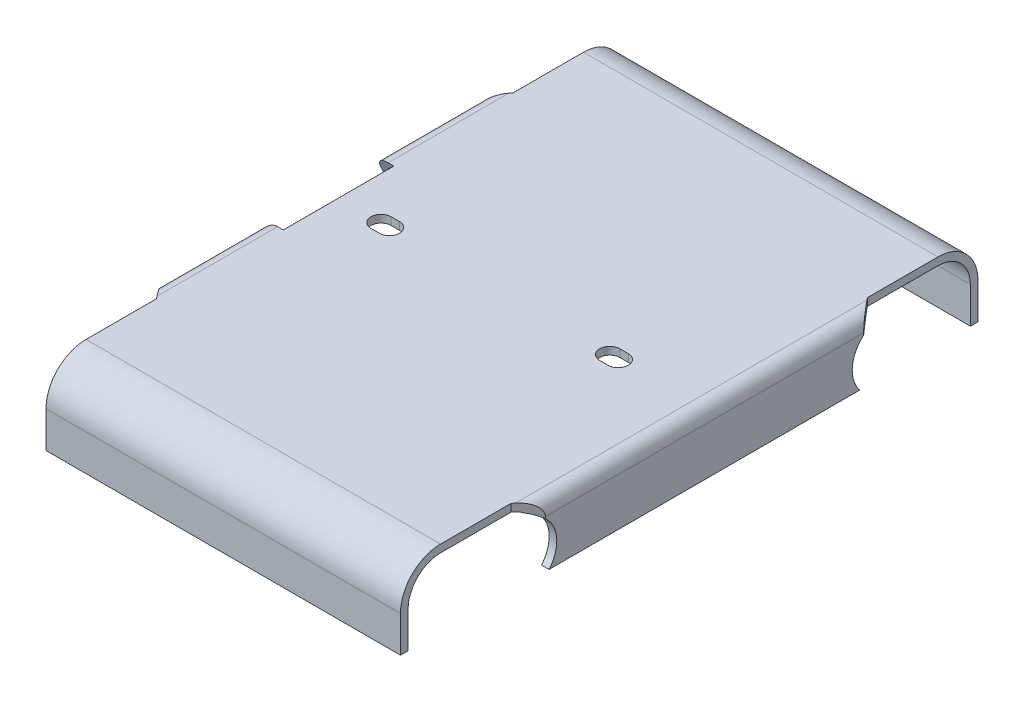
SolidWorks part; units mm, degrees
ref_plane "Plan de face" through (0, 0, 0) normal (0, 0, 1) x (1, 0, 0)
ref_plane "Plan de dessus" through (0, 0, 0) normal (0, 1, 0) x (1, 0, 0)
ref_plane "Plan de droite" through (0, 0, 0) normal (1, 0, 0) x (0, 0, -1)
sketch "Esquisse1" plane through (0, 0, 0) normal (0, 1, 0) x (1, 0, 0)
  line L0 (-60.4921, 0) -> (63.4192, 0) construction
  line L1 (-50.5, -75.75) -> (50.5, -75.75)
  line L2 (-50.5, -75.75) -> (-50.5, 75.75)
  line L3 (-50.5, 75.75) -> (50.5, 75.75)
  line L4 (50.5, -75.75) -> (50.5, 75.75)
  line L5 (0, 0) -> (0, 85.0821) construction
  dimension "D1" = 151.5
  dimension "D2" = 101
extrude "Extrusion1" add sketch "Esquisse1" against normal blind 20
fillet "Congé2" radius 10.5 2 edges at (0, 0, -75.75) (0, 0, 75.75)
fillet "Congé3" radius 3.5 10 edges at (-50.5, 0, 0) (50.5, 0, 0) (-50.5, -3.0754, 72.6746) (-50.5, -3.0754, -72.6746) (50.5, -3.0754, 72.6746) (50.5, -3.0754, -72.6746) (-50.5, -15.25, -75.75) (50.5, -15.25, -75.75) (50.5, -15.25, 75.75) (-50.5, -15.25, 75.75)
shell "Coque1" thickness 2
sketch "Esquisse5" plane through (0, 0, 0) normal (0, 1, 0) x (-1, 0, 0)
  line L0 (54.4782, 0) -> (-63.9785, 0) construction
  line L1 (47, -75.75) -> (-47, -75.75) construction
  line L2 (-46.5, -75.75) -> (-50.5, -75.75)
  line L3 (-46.5, -75.75) -> (-46.5, -46.75)
  line L5 (-50.5, -75.75) -> (-50.5, -41.75)
  line L6 (-46.5, -46.75) -> (-50.5, -41.75)
  line L7 (-50.5, -65.25) -> (-50.5, 65.25) construction
  line L8 (-46.5, 46.75) -> (-50.5, 41.75)
  line L9 (-50.5, 75.75) -> (-50.5, 41.75)
  line L10 (-46.5, 75.75) -> (-46.5, 46.75)
  line L11 (-46.5, 75.75) -> (-50.5, 75.75)
  line L12 (0, 0) -> (0, -89.9597) construction
  line L13 (46.5, 75.75) -> (50.5, 75.75)
  line L14 (46.5, 75.75) -> (46.5, 46.75)
  line L15 (50.5, 75.75) -> (50.5, 41.75)
  line L16 (46.5, 46.75) -> (50.5, 41.75)
  line L17 (46.5, -46.75) -> (50.5, -41.75)
  line L18 (50.5, -75.75) -> (50.5, -41.75)
  line L19 (46.5, -75.75) -> (46.5, -46.75)
  line L20 (46.5, -75.75) -> (50.5, -75.75)
  dimension "D1" = 4
  dimension "D2" = 34
  dimension "D3" = 5
extrude "Enlèv. mat.-Extru.4" cut sketch "Esquisse5" against normal through all
sketch "Esquisse2" plane through (0, 0, 0) normal (1, 0, 0) x (0, 0, -1)
  line L0 (0, 15.0146) -> (0, -24.9029) construction
  line L1 (-73.75, -10.5) -> (-73.75, -20)
  line L2 (-65.25, -2) -> (-47.25, -2)
  line L3 (-73.75, -20) -> (73.75, -20)
  line L5 (65.25, -2) -> (47.25, -2)
  line L6 (73.75, -10.5) -> (73.75, -20)
  line L7 (-41.75, -20) -> (41.75, -20) construction
  line L9 (-40.7693, -16) -> (40.7693, -16)
  line L10 (46.125, 0) -> (-46.125, 0) construction
  arc A0 (-65.25, -2) -> (-73.75, -10.5) centre (-65.25, -10.5) ccw
  arc A2 (-40.7693, -16) -> (-47.25, -2) centre (-47.25, -10.5) ccw
  arc A3 (40.7693, -16) -> (47.25, -2) centre (47.25, -10.5) cw
  arc A4 (65.25, -2) -> (73.75, -10.5) centre (65.25, -10.5) cw
  arc A5 (-65.25, -2) -> (-73.75, -10.5) centre (-65.25, -10.5) ccw construction
  dimension "D1" = 35
  dimension "D2" = 16
extrude "Enlèv. mat.-Extru.1" cut sketch "Esquisse2" against normal through all and the other way through all
sketch "Esquisse3" plane through (-50.5, 0, 0) normal (-1, 0, 0) x (0, 0, 1)
  line L0 (0, 7.4155) -> (0, -20.611) construction
  line L1 (-17.75, -16) -> (-17.75, -7)
  line L2 (-40.7693, -16) -> (40.7693, -16) construction
  line L3 (-17.75, -7) -> (-14.5, 0)
  line L4 (-46.125, 0) -> (46.125, 0) construction
  line L5 (17.75, -16) -> (17.75, -7)
  line L6 (17.75, -7) -> (14.5, 0)
  line L7 (-14.5, 0) -> (14.5, 0)
  line L8 (-17.75, -16) -> (17.75, -16)
  dimension "D1" = 35.5
  dimension "D2" = 29
  dimension "D3" = 9
extrude "Enlèv. mat.-Extru.2" cut sketch "Esquisse3" against normal blind 5
sketch "Esquisse6" plane through (0, 0, 0) normal (0, 1, 0) x (-1, 0, 0)
  line L0 (58.0409, 0) -> (-65.463, 0) construction
  line L1 (33.25, -8.7006) -> (33.25, 6.2394) construction
  line L2 (-25.65, 2.65) -> (-27.85, 2.65)
  line L3 (-50.5, -41.75) -> (-50.5, 41.75) construction
  line L4 (-25.65, -2.65) -> (-27.85, -2.65)
  line L5 (-26.75, -8.7006) -> (-26.75, 6.2394) construction
  line L6 (32.15, -2.65) -> (34.35, -2.65)
  line L7 (32.15, 2.65) -> (34.35, 2.65)
  arc A0 (-27.85, -2.65) -> (-27.85, 2.65) centre (-27.85, 0) cw
  arc A1 (-25.65, -2.65) -> (-25.65, 2.65) centre (-25.65, 0) ccw
  arc A2 (32.15, -2.65) -> (32.15, 2.65) centre (32.15, 0) cw
  arc A3 (34.35, -2.65) -> (34.35, 2.65) centre (34.35, 0) ccw
  dimension "D2" = 7.5
  dimension "D4" = 60
  dimension "D1" = 5.3
  dimension "D3" = 22.65
extrude "Enlèv. mat.-Extru.5" cut sketch "Esquisse6" against normal through all
